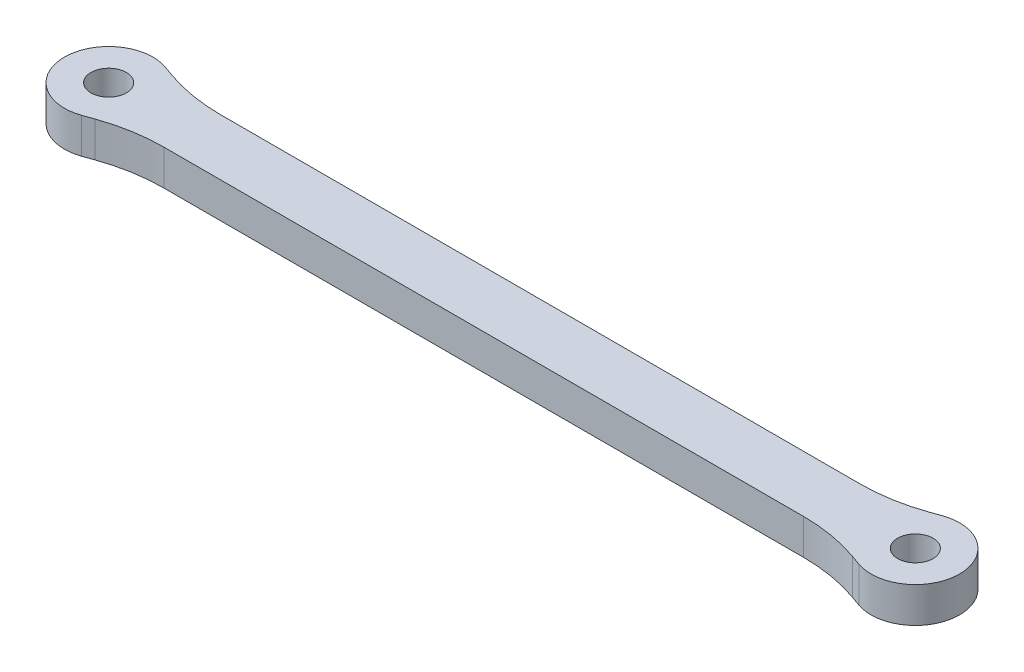
SolidWorks part; units mm, degrees
ref_plane "Front Plane" through (0, 0, 0) normal (0, 0, 1) x (1, 0, 0)
ref_plane "Top Plane" through (0, 0, 0) normal (0, 1, 0) x (1, 0, 0)
ref_plane "Right Plane" through (0, 0, 0) normal (1, 0, 0) x (0, 0, -1)
sketch "Sketch1" plane through (0, 0, 0) normal (0, 1, 0) x (1, 0, 0)
  line L0 (0, 0) -> (3, 0) construction
  line L1 (3, 0) -> (42.5, 0) construction
  line L2 (42.5, 0) -> (45.5, 0) construction
  line L3 (0.8333, 2.357) -> (3.0004, 1.5909)
  line L4 (3.0004, 1.5909) -> (42.4996, 1.5909)
  line L6 (3.0004, -1.5909) -> (42.4996, -1.5909)
  line L8 (0.8333, -2.357) -> (3.0004, -1.5909)
  line L9 (42.4996, 1.5909) -> (44.6667, 2.357)
  line L10 (42.4996, -1.5909) -> (44.6667, -2.357)
  circle A0 centre (0, 0) radius 1
  arc A1 (0.8333, 2.357) -> (0.8333, -2.357) centre (0, 0) ccw
  circle A2 centre (45.5, 0) radius 1
  arc A3 (44.6667, -2.357) -> (44.6667, 2.357) centre (45.5, 0) ccw
  circle A4 centre (3, 0) radius 1.5 construction
  circle A5 centre (42.5, 0) radius 1.5 construction
  dimension "D1" = 5
  dimension "D2" = 5
  dimension "D3" = 2
  dimension "D4" = 2
  dimension "D8" = 3
  dimension "D9" = 3
  dimension "D5" = 45.5
  dimension "D6" = 3
  dimension "D7" = 3
extrude "Boss-Extrude2" add sketch "Sketch1" along normal blind 2
fillet "Fillet2" radius 10 4 edges at (42.4996, 1, 1.5909) (42.4996, 1, -1.5909) (3.0004, 1, -1.5909) (3.0004, 1, 1.5909)
